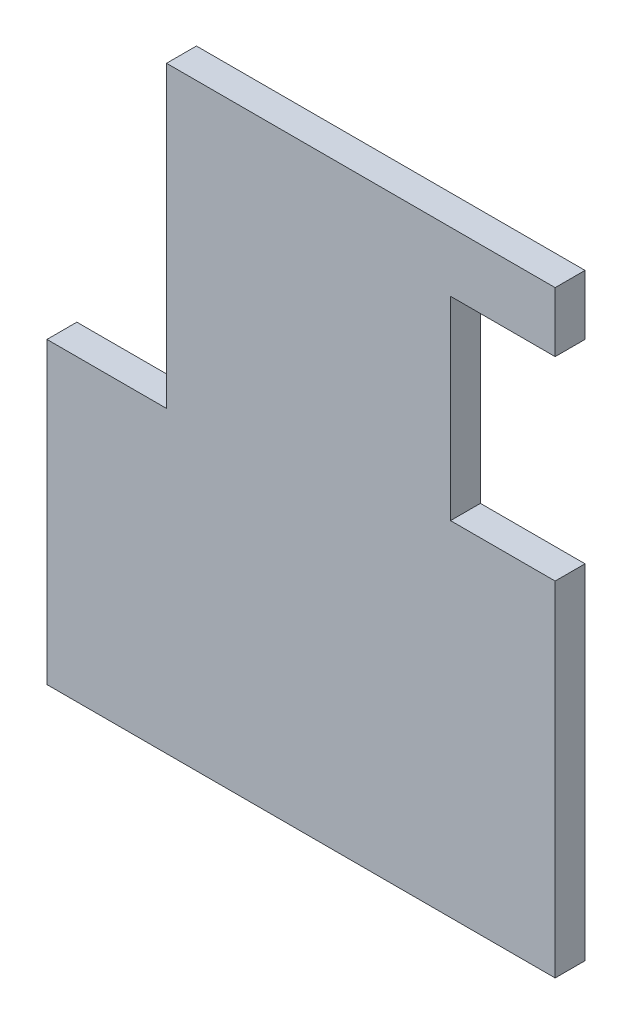
SolidWorks part; units mm, degrees
ref_plane "Front Plane" through (0, 0, 0) normal (0, 0, 1) x (1, 0, 0)
ref_plane "Top Plane" through (0, 0, 0) normal (0, 1, 0) x (1, 0, 0)
ref_plane "Right Plane" through (0, 0, 0) normal (1, 0, 0) x (0, 0, -1)
sketch "Sketch2" plane through (0, 0, 0) normal (0, 0, 1) x (1, 0, 0)
  line L0 (-89.0928, -29.4427) -> (80.9072, -29.4427)
  line L1 (80.9072, -29.4427) -> (80.9072, 85.5573)
  line L2 (80.9072, 170.5573) -> (-49.0928, 170.5573)
  line L3 (-49.0928, 170.5573) -> (-49.0928, 70.5573)
  line L4 (-49.0928, 70.5573) -> (-89.0928, 70.5573)
  line L5 (-89.0928, 70.5573) -> (-89.0928, -29.4427)
  line L7 (80.9072, 150.5573) -> (45.9072, 150.5573)
  line L8 (45.9072, 150.5573) -> (45.9072, 85.5573)
  line L9 (45.9072, 85.5573) -> (80.9072, 85.5573)
  line L10 (80.9072, 150.5573) -> (80.9072, 170.5573)
  dimension "D1" = 100
  dimension "D2" = 170
extrude "Boss-Extrude1" add sketch "Sketch2" along normal blind 10
